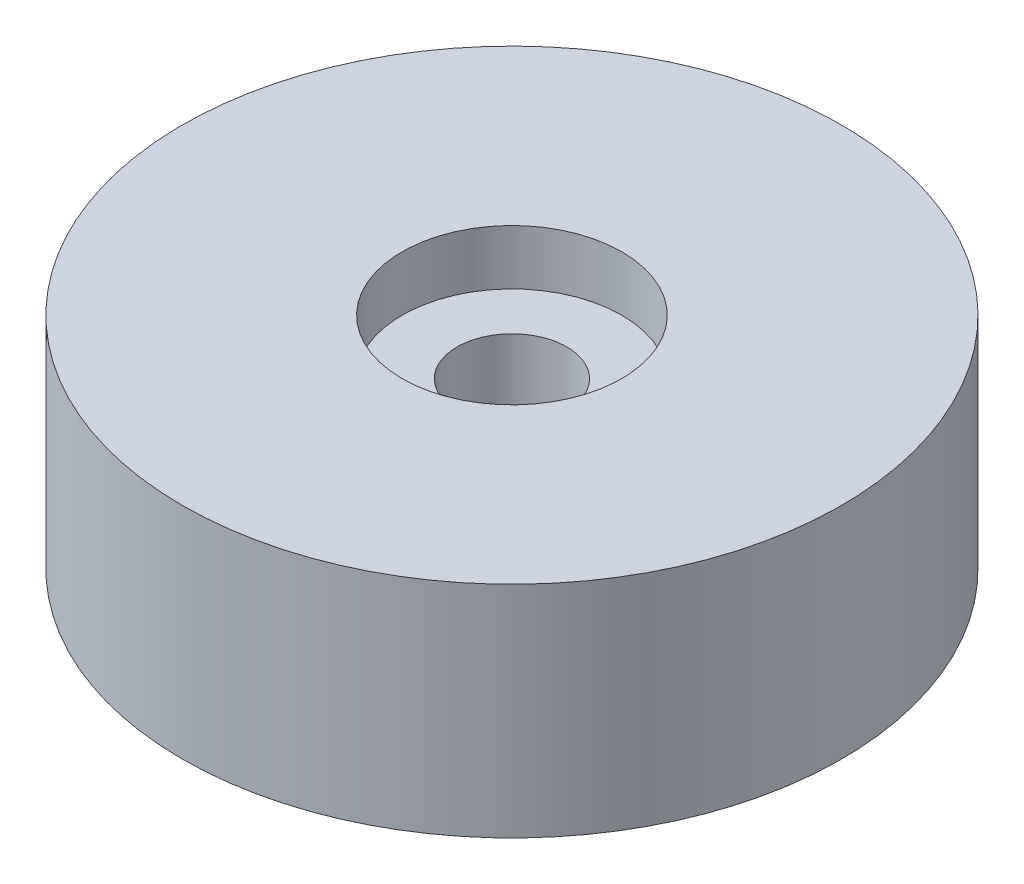
SolidWorks part; units mm, degrees
ref_plane "Front Plane" through (0, 0, 0) normal (0, 0, 1) x (1, 0, 0)
ref_plane "Top Plane" through (0, 0, 0) normal (0, 1, 0) x (1, 0, 0)
ref_plane "Right Plane" through (0, 0, 0) normal (1, 0, 0) x (0, 0, -1)
sketch "Sketch1" plane through (0, 0, 0) normal (0, 1, 0) x (1, 0, 0)
  circle A0 centre (0, 0) radius 19.05
  dimension "D1" = 38.1
extrude "Boss-Extrude1" add sketch "Sketch1" against normal blind 12.7
sketch "Sketch2" plane through (0, 0, 0) normal (0, 1, 0) x (1, 0, 0)
  circle A0 centre (0, 0) radius 3.175
  dimension "D1" = 6.35
extrude "Cut-Extrude1" cut sketch "Sketch2" against normal blind 17.78
sketch "Sketch3" plane through (0, 0, 0) normal (0, 1, 0) x (1, 0, 0)
  circle A0 centre (0, 0) radius 6.35
  dimension "D1" = 12.7
extrude "Cut-Extrude2" cut sketch "Sketch3" against normal blind 3.175
